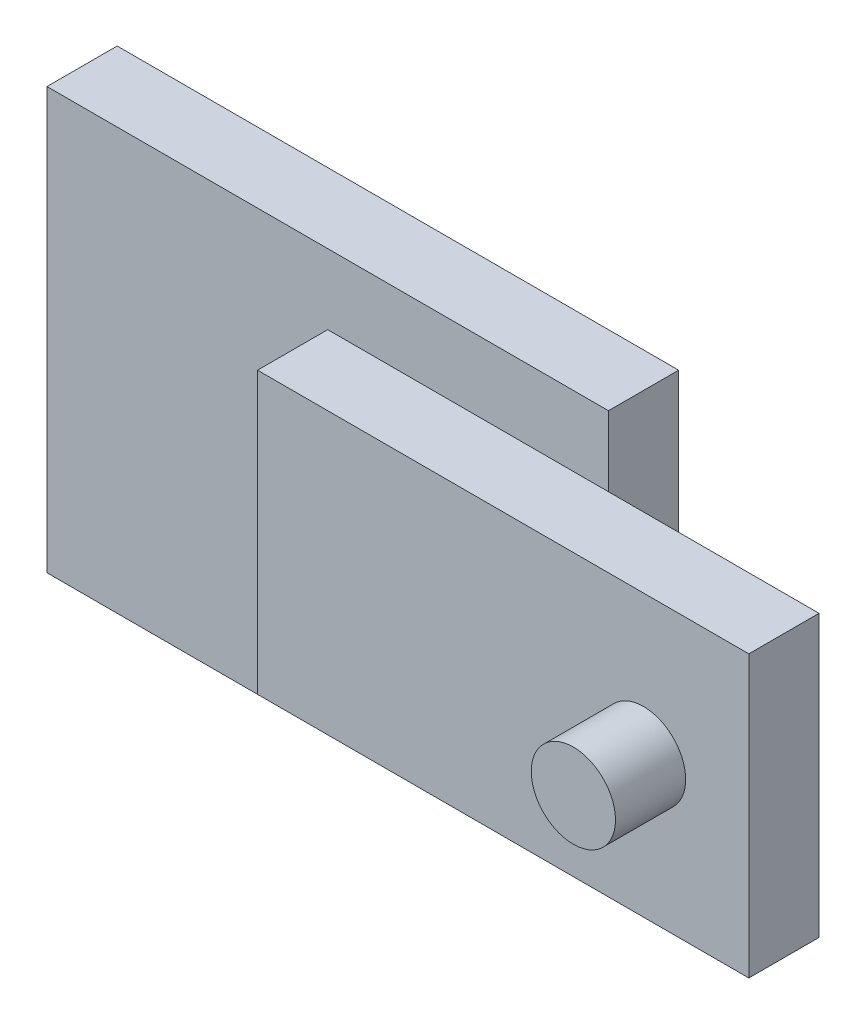
SolidWorks part; units mm, degrees
material "ABS"
ref_plane "Alzado" through (0, 0, 0) normal (0, 0, 1) x (1, 0, 0)
ref_plane "Planta" through (0, 0, 0) normal (0, 1, 0) x (1, 0, 0)
ref_plane "Vista lateral" through (0, 0, 0) normal (1, 0, 0) x (0, 0, -1)
sketch "Croquis1" plane through (0, 0, 0) normal (0, 0, 1) x (1, 0, 0)
  line L1 (-40, -30) -> (40, -30)
  line L2 (-40, -30) -> (-40, 30)
  line L3 (-40, 30) -> (40, 30)
  line L4 (40, -30) -> (40, 30)
  line L5 (-40, -30) -> (40, 30) construction
  line L6 (-40, 30) -> (40, -30) construction
  point P0 (0, 0)
  dimension "D1" = 60
  dimension "D2" = 80
extrude "Saliente-Extruir1" add sketch "Croquis1" along normal blind 10
sketch "Croquis2" plane through (0, 0, 10) normal (0, 0, 1) x (1, 0, 0)
  line L0 (0, 0) -> (40, 0) construction
  line L1 (40, -30) -> (40, 30) construction
  line L2 (0, -20) -> (0, 20)
  line L3 (0, 20) -> (70, 20)
  line L4 (70, 20) -> (70, -20)
  line L5 (0, -20) -> (70, -20)
  point P9 (70, 0)
  dimension "D1" = 20
  dimension "D2" = 70
extrude "Saliente-Extruir2" add sketch "Croquis2" along normal blind 10
sketch "Croquis3" plane through (0, 0, 20) normal (0, 0, 1) x (1, 0, 0)
  line L0 (70, 0) -> (55, 0) construction
  line L1 (70, -20) -> (70, 20) construction
  circle A0 centre (55, 0) radius 6
  dimension "D2" = 12
  dimension "D1" = 15
extrude "Saliente-Extruir3" add sketch "Croquis3" along normal blind 10
